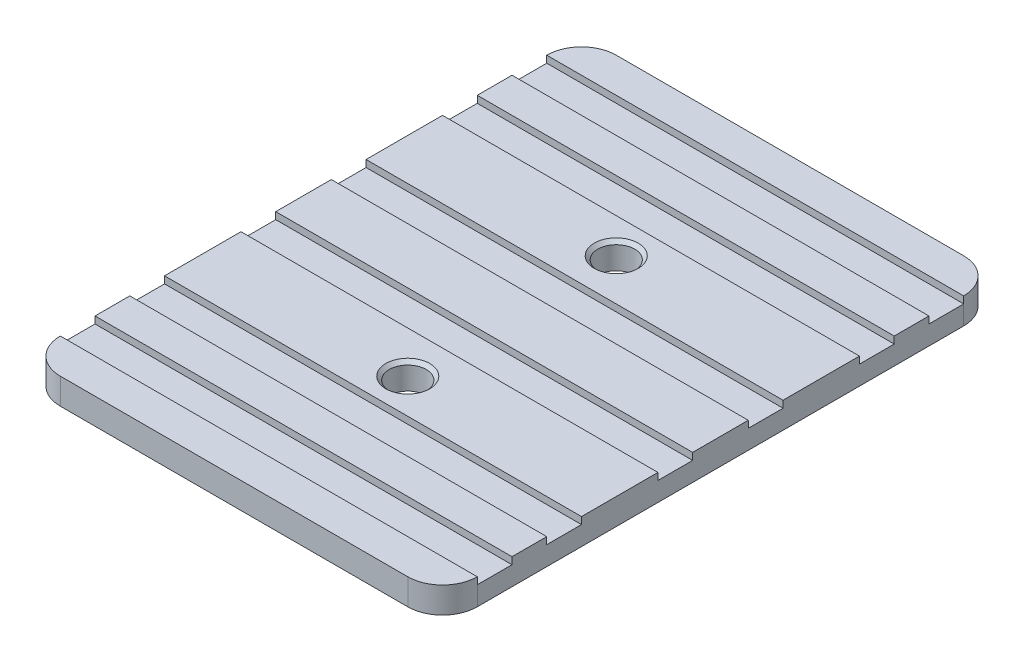
SolidWorks part; units mm, degrees
ref_plane "Front Plane" through (0, 0, 0) normal (0, 0, 1) x (1, 0, 0)
ref_plane "Top Plane" through (0, 0, 0) normal (0, 1, 0) x (1, 0, 0)
ref_plane "Right Plane" through (0, 0, 0) normal (1, 0, 0) x (0, 0, -1)
sketch "Sketch1" plane through (0, 0, 0) normal (0, 1, 0) x (1, 0, 0)
  line L1 (0, 0) -> (76.2, 0)
  line L2 (0, 0) -> (0, -101.6)
  line L3 (0, -101.6) -> (76.2, -101.6)
  line L4 (76.2, 0) -> (76.2, -101.6)
  dimension "D1" = 76.2
  dimension "D2" = 101.6
extrude "Boss-Extrude1" add sketch "Sketch1" along normal blind 4.7625
sketch "Sketch2" plane through (0, 4.7625, 0) normal (0, 1, 0) x (1, 0, 0)
  line L0 (0, -50.8) -> (76.2, -50.8) construction
  line L1 (0, 0) -> (0, -101.6) construction
  line L2 (76.2, -101.6) -> (76.2, 0) construction
  line L3 (38.1, 0) -> (38.1, -101.6) construction
  line L4 (38.1, -50.8) -> (38.1, -101.6) construction
  line L5 (0, -101.6) -> (76.2, -101.6) construction
  line L6 (76.2, 0) -> (0, 0) construction
  line L7 (0, -31.75) -> (76.2, -31.75) construction
  point P6 (38.1, -31.75)
  point P18 (38.1, -69.85)
  dimension "D1" = 19.05
hole_wizard "1/4 Clearance Hole1" positions "Sketch2" profile "Sketch3" hole size "1/4" standard "ANSI Inch" end condition through all
sketch "Sketch3" plane through (38.1, 4.7625, 69.85) normal (1, 0, 0) x (0, 0, 1)
  line L0 (0, 0) -> (0, 4.7625)
  line L1 (0, 4.7625) -> (3.3782, 4.7625)
  line L2 (3.3782, 4.7625) -> (3.3782, 0.635)
  line L3 (3.3782, 0.635) -> (4.0132, 0)
  line L5 (4.0132, 0) -> (0, 0)
  line L6 (-3.3782, 0.635) -> (-4.0132, 0) construction
  line L11 (0, -6.35) -> (0, 107.95) construction
  dimension "Thru Hole Dia." = 6.7564
  dimension "Thru Hole Depth" = 4.7625
  dimension "Near C'Sink Dia." = 8.0264
  dimension "Near C'Sink Angle" = 90
fillet "Fillet1" radius 6.35 4 edges at (0, 2.3813, 0) (0, 2.3813, 101.6) (76.2, 2.3813, 101.6) (76.2, 2.3813, 0)
sketch "Sketch7" plane through (0, 4.7625, 0) normal (0, 1, 0) x (1, 0, 0)
  line L0 (0, -6.35) -> (76.2, -6.35)
  line L1 (0, -12.7) -> (76.2, -12.7)
  line L2 (0, -39.37) -> (76.2, -39.37)
  line L3 (0, -45.72) -> (76.2, -45.72)
  line L12 (0, -55.88) -> (76.2, -55.88)
  line L13 (0, -62.23) -> (76.2, -62.23)
  line L14 (0, -88.9) -> (76.2, -88.9)
  line L15 (0, -95.25) -> (76.2, -95.25)
  line L16 (0, -6.35) -> (0, -12.7)
  line L17 (0, -39.37) -> (0, -45.72)
  line L18 (0, -55.88) -> (0, -62.23)
  line L19 (0, -88.9) -> (0, -95.25)
  line L20 (76.2, -95.25) -> (76.2, -88.9)
  line L21 (76.2, -62.23) -> (76.2, -55.88)
  line L22 (76.2, -45.72) -> (76.2, -39.37)
  line L23 (76.2, -12.7) -> (76.2, -6.35)
  line L24 (69.85, 0) -> (6.35, 0) construction
  line L25 (6.35, -101.6) -> (69.85, -101.6) construction
  line L26 (0, -50.8) -> (76.2, -50.8) construction
  line L27 (0, -6.35) -> (0, -95.25) construction
  line L28 (76.2, -95.25) -> (76.2, -6.35) construction
  line L29 (0, -76.2) -> (0, -82.55)
  line L30 (0, -82.55) -> (76.2, -82.55)
  line L31 (76.2, -82.55) -> (76.2, -76.2)
  line L32 (76.2, -76.2) -> (0, -76.2)
  line L33 (76.2, -19.05) -> (76.2, -25.4)
  line L34 (0, -19.05) -> (76.2, -19.05)
  line L35 (0, -25.4) -> (0, -19.05)
  line L36 (76.2, -25.4) -> (0, -25.4)
  dimension "D1" = 6.35
  dimension "D2" = 6.35
  dimension "D3" = 6.35
  dimension "D4" = 10.16
  dimension "D5" = 6.35
  dimension "D6" = 6.35
extrude "Cut-Extrude1" cut sketch "Sketch7" against normal blind 1.27
